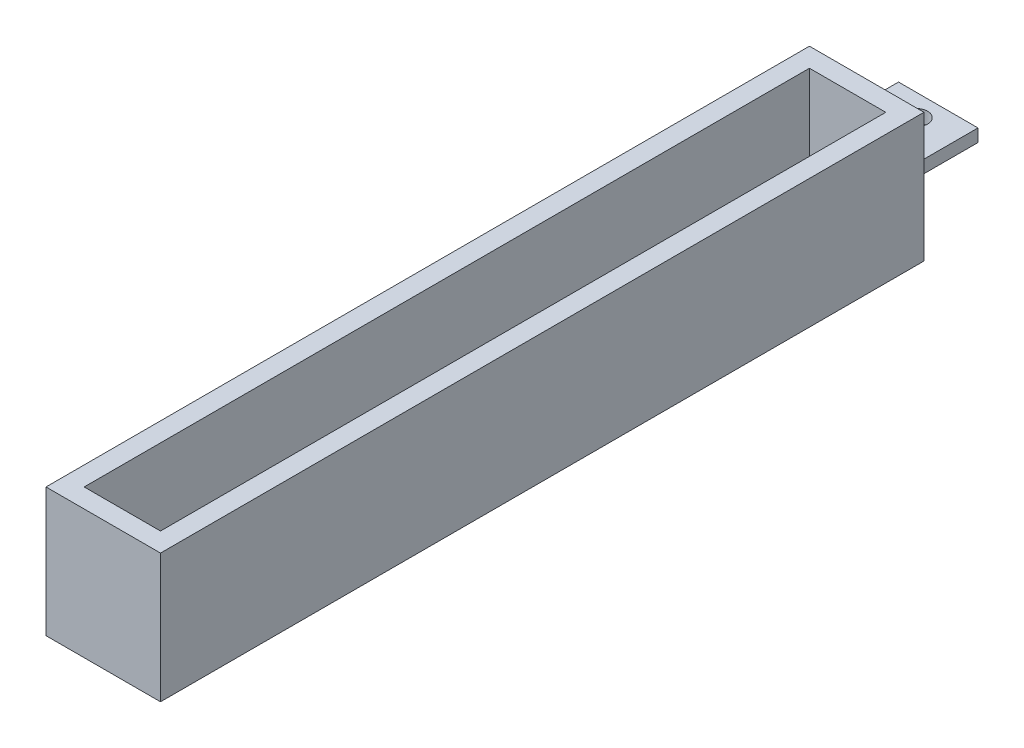
SolidWorks part; units mm, degrees
ref_plane "Front Plane" through (0, 0, 0) normal (0, 0, 1) x (1, 0, 0)
ref_plane "Top Plane" through (0, 0, 0) normal (0, 1, 0) x (1, 0, 0)
ref_plane "Right Plane" through (0, 0, 0) normal (1, 0, 0) x (0, 0, -1)
sketch "Sketch1" plane through (0, 0, 0) normal (0, 0, 1) x (1, 0, 0)
  line L1 (0, 0) -> (24, 0)
  line L2 (0, 0) -> (0, 27)
  line L3 (0, 27) -> (24, 27)
  line L4 (24, 0) -> (24, 27)
  dimension "D1" = 24
  dimension "D2" = 27
extrude "Boss-Extrude1" add sketch "Sketch1" along normal blind 160
shell "Shell1" thickness 4
sketch "Sketch2" plane through (0, 0, 0) normal (0, 0, -1) x (-1, 0, 0)
  line L0 (-12, 27) -> (-12, 14.8278) construction
  line L1 (-3.672, 14.8278) -> (-20.328, 14.8278)
  line L2 (-3.672, 14.8278) -> (-3.672, 12.1722)
  line L3 (-3.672, 12.1722) -> (-20.328, 12.1722)
  line L4 (-20.328, 14.8278) -> (-20.328, 12.1722)
  line L5 (-24, 27) -> (0, 27) construction
  line L6 (-12, 12.1722) -> (-12, 0) construction
  line L7 (0, 0) -> (-24, 0) construction
extrude "Boss-Extrude2" add sketch "Sketch2" along normal blind 15
sketch "Sketch3" plane through (0, 14.8278, 0) normal (0, 1, 0) x (1, 0, 0)
  line L0 (12, 15) -> (12, 10.4031) construction
  line L1 (3.672, 15) -> (20.328, 15) construction
  line L2 (12, 10.4031) -> (12, 0) construction
  line L3 (24, 0) -> (0, 0) construction
  circle A0 centre (12, 10.4031) radius 2.352
extrude "Cut-Extrude1" cut sketch "Sketch3" against normal through all
